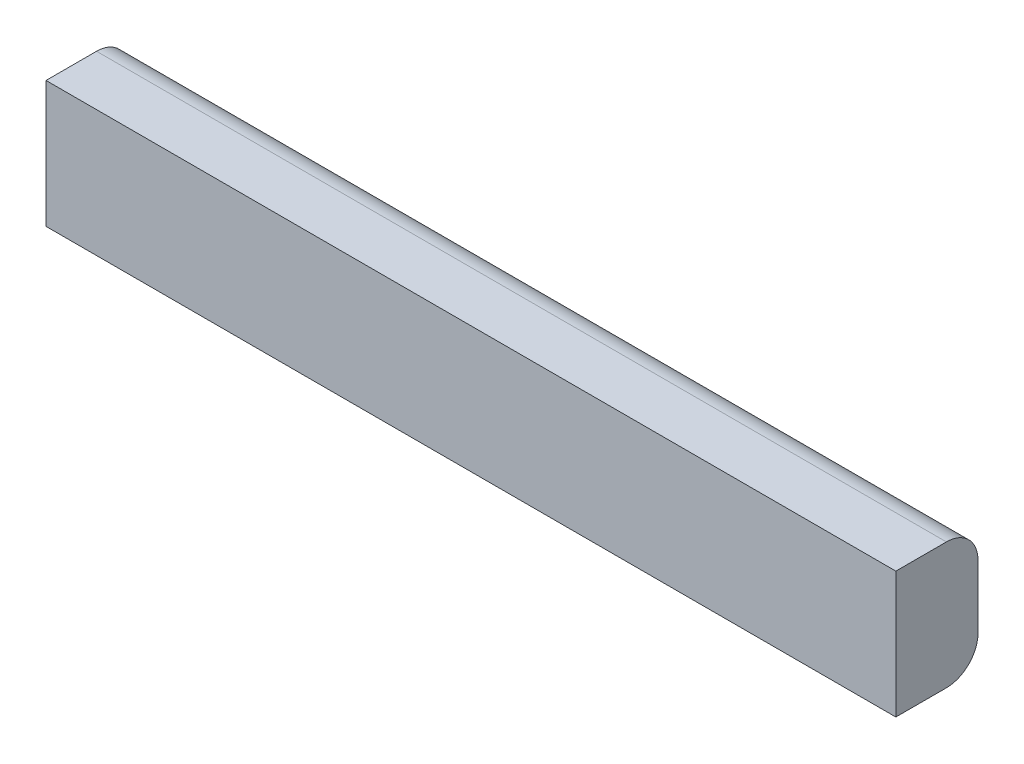
SolidWorks part; units mm, degrees
ref_plane "Front Plane" through (0, 0, 0) normal (0, 0, 1) x (1, 0, 0)
ref_plane "Top Plane" through (0, 0, 0) normal (0, 1, 0) x (1, 0, 0)
ref_plane "Right Plane" through (0, 0, 0) normal (1, 0, 0) x (0, 0, -1)
sketch "Sketch1" plane through (0, 0, 0) normal (1, 0, 0) x (0, 0, -1)
  line L1 (49.3736, 66.0217) -> (-1.4264, 66.0217)
  line L2 (81.1236, 34.2717) -> (81.1236, -29.2283)
  line L3 (49.3736, -60.9783) -> (-1.4264, -60.9783)
  line L4 (-1.4264, 66.0217) -> (-1.4264, -60.9783)
  arc A0 (49.3736, 66.0217) -> (81.1236, 34.2717) centre (49.3736, 34.2717) cw
  arc A1 (81.1236, -29.2283) -> (49.3736, -60.9783) centre (49.3736, -29.2283) cw
  point P8 (81.1236, -60.9783)
  dimension "D3" = 31.75
  dimension "D1" = 127
extrude "Boss-Extrude1" add sketch "Sketch1" along normal mid plane 853.948
equation "\"bumple\"= 24in'bumpler length"
equation "\"D1@Boss-Extrude1\"=\"bumple\""
